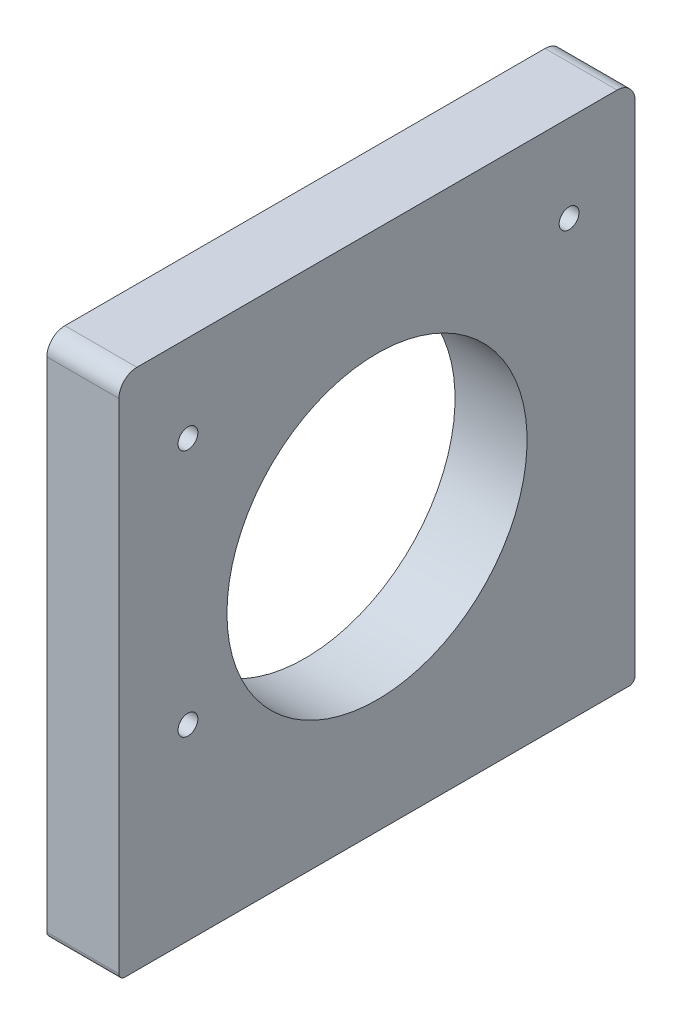
SolidWorks part; units mm, degrees
ref_plane "Front Plane" through (0, 0, 0) normal (0, 0, 1) x (1, 0, 0)
ref_plane "Top Plane" through (0, 0, 0) normal (0, 1, 0) x (1, 0, 0)
ref_plane "Right Plane" through (0, 0, 0) normal (1, 0, 0) x (0, 0, -1)
sketch "Sketch1" plane through (0, 0, 0) normal (0, 1, 0) x (1, 0, 0)
  line L1 (0, 0) -> (40, 0)
  line L2 (0, 0) -> (0, -86)
  line L3 (0, -86) -> (40, -86)
  line L4 (40, 0) -> (40, -86)
  dimension "D1" = 40
  dimension "D2" = 86
extrude "Boss-Extrude1" add sketch "Sketch1" along normal blind 12
sketch "Sketch2" plane through (0, 12, 0) normal (0, 1, 0) x (1, 0, 0)
  line L0 (0, -86) -> (40, -86) construction
  line L1 (40, 0) -> (28, 0)
  line L2 (40, 0) -> (40, -86)
  line L3 (40, -86) -> (28, -86)
  line L4 (28, 0) -> (28, -86)
  dimension "D1" = 12
extrude "Boss-Extrude2" add sketch "Sketch2" along normal blind 87
sketch "Sketch3" plane through (0, 12, 0) normal (0, 1, 0) x (1, 0, 0)
  line L0 (0, -43) -> (62.3366, -43) construction
  line L1 (0, 0) -> (0, -86) construction
  circle A0 centre (14, -8.4) radius 3
  circle A1 centre (14, -77.6) radius 3
  dimension "D1" = 34.6
  dimension "D2" = 6
  dimension "D3" = 14
extrude "Cut-Extrude1" cut sketch "Sketch3" against normal through all
sketch "Sketch5" plane through (28, 0, 0) normal (-1, 0, 0) x (0, 0, 1)
  circle A0 centre (74.5, 84.5) radius 1.65
  circle A1 centre (74.5, 43.2) radius 1.65
  circle A2 centre (11, 84.5) radius 1.65
  dimension "D1" = 3.3
extrude "Cut-Extrude3" cut sketch "Sketch5" against normal through all
fillet "Fillet1" radius 3 2 edges at (34, 99, 86) (34, 99, 0)
sketch "Sketch6" plane through (28, 0, 0) normal (-1, 0, 0) x (0, 0, 1)
  circle A0 centre (43, 56) radius 25
  dimension "D1" = 50
extrude "Cut-Extrude4" cut sketch "Sketch6" against normal through all
sketch "Sketch7" plane through (0, 0, 86) normal (0, 0, 1) x (1, 0, 0)
  line L1 (40, 0) -> (0, 0)
  line L2 (40, 0) -> (40, 12)
  line L3 (40, 12) -> (0, 12)
  line L4 (0, 0) -> (0, 12)
extrude "Cut-Extrude5" cut sketch "Sketch7" against normal through all
sketch "Sketch8" plane through (0, 12, 0) normal (0, -1, 0) x (1, 0, 0)
  circle A0 centre (34, 76) radius 2.1
  circle A1 centre (34, 10) radius 2.1
  point P6 (0, 0)
  point P7 (0, 0)
  point P8 (34, 76)
  point P10 (34, 10)
  dimension "D1" = 4.2
extrude "Cut-Extrude6" cut sketch "Sketch8" against normal blind 12
fillet "Fillet2" radius 1 2 edges at (34, 12, 0) (34, 12, 86)
